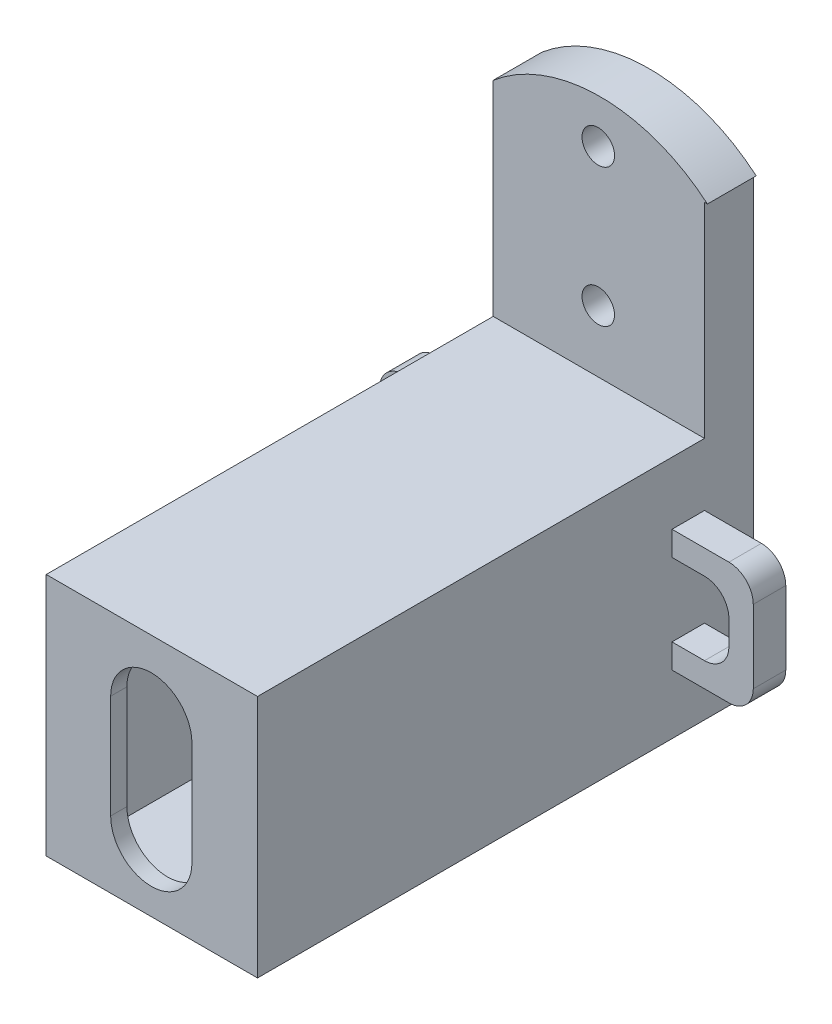
SolidWorks part; units mm, degrees
material "ABS PC"
ref_plane "Front Plane" through (0, 0, 0) normal (0, 0, 1) x (1, 0, 0)
ref_plane "Top Plane" through (0, 0, 0) normal (0, 1, 0) x (1, 0, 0)
ref_plane "Right Plane" through (0, 0, 0) normal (1, 0, 0) x (0, 0, -1)
sketch "Sketch1" plane through (0, 0, 0) normal (0, 0, 1) x (1, 0, 0)
  line L1 (8.0353, -13.0573) -> (-7.9647, -13.0573)
  line L2 (8.0353, -13.0573) -> (8.0353, 13.1729)
  line L4 (-7.9647, -13.0573) -> (-7.9647, 12.9427)
  line L5 (8.0353, -13.0573) -> (-7.9647, 12.9427) construction
  line L6 (8.0353, 13.1729) -> (-7.9647, -13.0573) construction
  arc A0 (-7.9647, 12.9427) -> (8.0353, 13.1729) centre (0.1258, 6.7633) cw
  point P0 (0, 0)
  point P7 (-0.0206, 16.9427)
  dimension "D1" = 26
  dimension "D2" = 16
  dimension "D3" = 30
extrude "Boss-Extrude1" add sketch "Sketch1" along normal blind 3
sketch "Sketch2" plane through (0, 0, 3) normal (0, 0, 1) x (1, 0, 0)
  line L0 (-7.9647, -13.0573) -> (8.0353, -13.0573) construction
  line L1 (-6.4647, 1.9427) -> (6.5353, 1.9427)
  line L2 (-6.4647, 1.9427) -> (-6.4647, -13.0573)
  line L3 (-6.4647, -13.0573) -> (6.5353, -13.0573)
  line L4 (6.5353, 1.9427) -> (6.5353, -13.0573)
  line L5 (8.0353, -13.0573) -> (8.0353, 13.1729) construction
  dimension "D1" = 13
  dimension "D2" = 15
  dimension "D3" = 0
  dimension "D4" = 1.5
extrude "Boss-Extrude2" add sketch "Sketch2" along normal blind 27.5
sketch "Sketch3" plane through (0, 0, 3) normal (0, 0, 1) x (1, 0, 0)
  line L0 (6.5353, 1.9427) -> (-6.4647, 1.9427) construction
  line L1 (-5.3147, 0.6927) -> (5.2853, 0.6927)
  line L2 (-5.3147, 0.6927) -> (-5.3147, -12.3073)
  line L3 (-5.3147, -12.3073) -> (5.2853, -12.3073)
  line L4 (5.2853, 0.6927) -> (5.2853, -12.3073)
  line L6 (6.5353, -13.0573) -> (6.5353, 1.9427) construction
  dimension "D1" = 10.6
  dimension "D2" = 13
  dimension "D3" = 1.25
  dimension "D4" = 1.25
extrude "Cut-Extrude1" cut sketch "Sketch3" against normal mid plane 53
sketch "Sketch4" plane through (0, 0, 30.5) normal (0, 0, 1) x (1, 0, 0)
  line L0 (0, -8.9415) -> (0, -2.5597) construction
  line L1 (-2.5, -8.9415) -> (-2.5, -2.5597)
  line L2 (2.5, -8.9415) -> (2.5, -2.5597)
  arc A0 (-2.5, -8.9415) -> (2.5, -8.9415) centre (0, -8.9415) ccw
  arc A1 (2.5, -2.5597) -> (-2.5, -2.5597) centre (0, -2.5597) ccw
  point P3 (0, -5.7506)
  dimension "D1" = 2.5
extrude "Cut-Extrude2" cut sketch "Sketch4" against normal through all
sketch "Sketch5" plane through (0, 0, 3) normal (0, 0, 1) x (1, 0, 0)
  line L1 (-7.9647, -13.0573) -> (-6.4647, -13.0573)
  line L2 (-7.9647, -13.0573) -> (-7.9647, 14.5226)
  line L3 (-7.9647, 14.5226) -> (-6.4647, 14.5226)
  line L4 (-6.4647, -13.0573) -> (-6.4647, 14.5226)
  line L5 (6.5353, -13.0573) -> (8.0353, -13.0573)
  line L6 (6.5353, -13.0573) -> (6.5353, 14.5226)
  line L7 (6.5353, 14.5226) -> (8.0353, 14.5226)
  line L8 (8.0353, -13.0573) -> (8.0353, 14.5226)
  arc A0 (8.0353, 13.1729) -> (-7.9647, 12.9427) centre (0.1258, 6.7633) ccw construction
extrude "Cut-Extrude3" cut sketch "Sketch5" against normal through all
sketch "Sketch6" plane through (0, 0, 3) normal (0, 0, 1) x (1, 0, 0)
  line L0 (-6.4647, 1.9427) -> (6.5353, -13.0573) construction
  line L1 (6.5353, 1.9427) -> (-6.4647, -13.0573) construction
  line L2 (-15.1186, -5.6487) -> (16.3811, -5.6487) construction
  line L3 (6.5353, -3.3987) -> (10.0353, -3.3987)
  line L4 (6.5353, -13.0573) -> (6.5353, 1.9427) construction
  line L5 (10.0353, -3.3987) -> (10.0353, -7.8987)
  line L6 (10.0353, -7.8987) -> (6.5353, -7.8987)
  line L8 (6.5353, -3.3987) -> (6.5353, -5.6487)
  line L9 (11.5353, -9.3987) -> (6.5353, -9.3987)
  line L10 (11.5353, -1.8987) -> (11.5353, -9.3987)
  line L11 (6.5353, -1.8987) -> (11.5353, -1.8987)
  line L13 (5.0353, -1.8987) -> (5.0353, -9.3987) construction
  line L14 (6.5353, -7.8987) -> (6.5353, -9.3987)
  line L15 (6.5353, -3.3987) -> (6.5353, -1.8987)
  line L16 (6.5353, -3.3987) -> (6.5353, -7.8987) construction
  line L17 (5.0353, -1.8987) -> (11.5353, -1.8987) construction
  line L18 (11.5353, -9.3987) -> (5.0353, -9.3987) construction
  line L28 (0.0353, -3.0972) -> (0.0353, -9.3987) construction
  line L37 (-6.4647, -3.3987) -> (-9.9647, -3.3987)
  line L38 (-9.9647, -3.3987) -> (-9.9647, -7.8987)
  line L39 (-9.9647, -7.8987) -> (-6.4647, -7.8987)
  line L40 (-6.4647, -7.8987) -> (-6.4647, -9.3987)
  line L41 (-11.4647, -9.3987) -> (-6.4647, -9.3987)
  line L42 (-11.4647, -1.8987) -> (-11.4647, -9.3987)
  line L43 (-6.4647, -1.8987) -> (-11.4647, -1.8987)
  line L44 (-6.4647, -3.3987) -> (-6.4647, -1.8987)
  dimension "D1" = 3.5
  dimension "D2" = 4.5
  dimension "D3" = 2.25
  dimension "D4" = 1.5
extrude "Boss-Extrude4" add sketch "Sketch6" along normal blind 2 contours L37 L44 L43 L42 L41 L40 L39 L38 | L15 L3 L5 L6 L14 L9 L10 L11
fillet "Fillet2" radius 1.5 4 edges at (-9.9647, -3.3987, 4) (-9.9647, -7.8987, 4) (-11.4647, -9.3987, 4) (-11.4647, -1.8987, 4)
fillet "Fillet3" radius 1.5 4 edges at (10.0353, -3.3987, 4) (10.0353, -7.8987, 4) (11.5353, -9.3987, 4) (11.5353, -1.8987, 4)
sketch "Sketch7" plane through (0, 0, 3) normal (0, 0, 1) x (1, 0, 0)
  circle A0 centre (0, 14.2343) radius 1
  circle A1 centre (0, 5.7481) radius 1
  dimension "D1" = 2
  dimension "D2" = 2
extrude "Cut-Extrude4" cut sketch "Sketch7" against normal through all
